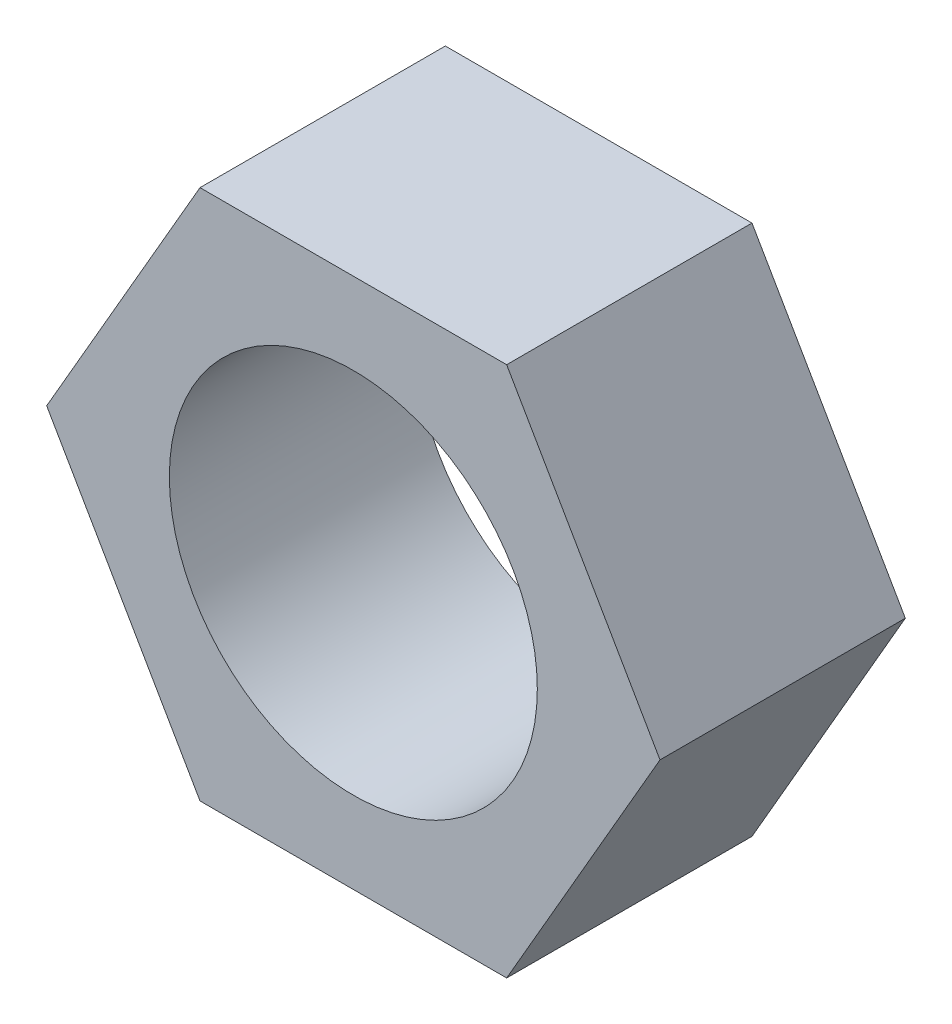
SolidWorks part; units mm, degrees
ref_plane "Alzado" through (0, 0, 0) normal (0, 0, 1) x (1, 0, 0)
ref_plane "Planta" through (0, 0, 0) normal (0, 1, 0) x (1, 0, 0)
ref_plane "Vista lateral" through (0, 0, 0) normal (1, 0, 0) x (0, 0, -1)
sketch "Croquis2" plane through (0, 0, 0) normal (0, 0, 1) x (1, 0, 0)
  line L1 (5, 0) -> (2.5, 4.3301)
  line L2 (2.5, 4.3301) -> (-2.5, 4.3301)
  line L3 (-2.5, 4.3301) -> (-5, 0)
  line L4 (-5, 0) -> (-2.5, -4.3301)
  line L5 (-2.5, -4.3301) -> (2.5, -4.3301)
  line L6 (2.5, -4.3301) -> (5, 0)
  circle A0 centre (0, 0) radius 4.3301 construction
  dimension "D1" = 5
extrude "Saliente-Extruir1" add sketch "Croquis2" along normal blind 4
sketch "Croquis3" plane through (0, 0, 0) normal (0, 0, -1) x (-1, 0, 0)
  circle A0 centre (0, 0) radius 3
extrude "Cortar-Extruir1" cut sketch "Croquis3" against normal through all
